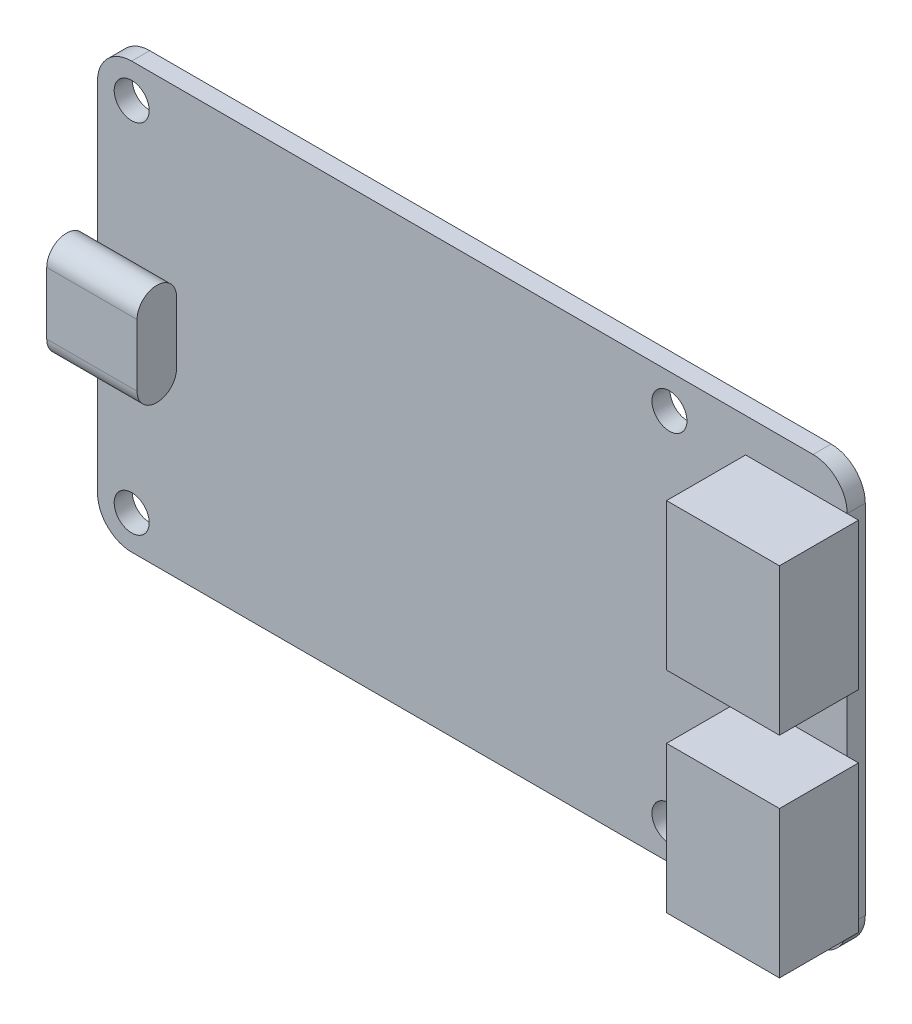
SolidWorks part; units mm, degrees
ref_plane "Plano frontal" through (0, 0, 0) normal (0, 0, 1) x (1, 0, 0)
ref_plane "Plano superior" through (0, 0, 0) normal (0, 1, 0) x (1, 0, 0)
ref_plane "Plano direito" through (0, 0, 0) normal (1, 0, 0) x (0, 0, -1)
sketch "Esboço1" plane through (0, 0, 0) normal (0, 0, 1) x (1, 0, 0)
  line L1 (-30.175, 18.835) -> (30.175, 18.835)
  line L2 (-33.2, 15.81) -> (-33.2, -15.81)
  line L3 (-30.175, -18.835) -> (30.175, -18.835)
  line L4 (33.2, 15.81) -> (33.2, -15.81)
  line L5 (-33.2, 18.835) -> (33.2, -18.835) construction
  line L6 (-33.2, -18.835) -> (33.2, 18.835) construction
  arc A0 (-33.2, -15.81) -> (-30.175, -18.835) centre (-30.175, -15.81) ccw
  arc A1 (30.175, -18.835) -> (33.2, -15.81) centre (30.175, -15.81) ccw
  arc A2 (30.175, 18.835) -> (33.2, 15.81) centre (30.175, 15.81) cw
  arc A3 (-30.175, 18.835) -> (-33.2, 15.81) centre (-30.175, 15.81) ccw
  circle A4 centre (-30.175, 15.81) radius 1.55
  circle A5 centre (-30.175, -15.81) radius 1.55
  circle A6 centre (17.455, 15.81) radius 1.55
  circle A7 centre (17.455, -15.81) radius 1.55
  point P0 (0, 0)
  dimension "D1" = 31.62
  dimension "D5" = 3.1
  dimension "D2" = 37.67
  dimension "D3" = 66.4
  dimension "D4" = 47.63
extrude "Ressalto-extrusão1" add sketch "Esboço1" along normal blind 1.6
sketch "Esboço2" plane through (0, 0, 1.6) normal (0, 0, 1) x (1, 0, 0)
  line L0 (0, 0) -> (18.5434, 0) construction
  line L1 (24.2, 15.81) -> (34.2, 15.81)
  line L2 (24.2, 15.81) -> (24.2, 2.81)
  line L3 (24.2, 2.81) -> (34.2, 2.81)
  line L4 (34.2, 15.81) -> (34.2, 2.81)
  line L5 (24.2, 15.81) -> (34.2, 2.81) construction
  line L6 (24.2, 2.81) -> (34.2, 15.81) construction
  line L7 (24.2, -2.81) -> (34.2, -15.81) construction
  line L8 (24.2, -15.81) -> (34.2, -2.81) construction
  line L9 (34.2, -15.81) -> (34.2, -2.81)
  line L10 (24.2, -2.81) -> (34.2, -2.81)
  line L11 (24.2, -15.81) -> (24.2, -2.81)
  line L12 (24.2, -15.81) -> (34.2, -15.81)
  line L13 (33.2, -15.81) -> (33.2, 15.81) construction
  point P0 (29.2, 9.31)
  point P12 (29.2, -9.31)
  dimension "D1" = 31.62
  dimension "D2" = 13
  dimension "D3" = 10
  dimension "D4" = 1
extrude "Ressalto-extrusão2" add sketch "Esboço2" along normal blind 7
sketch "Esboço3" plane through (-33.2, 0, 0) normal (-1, 0, 0) x (0, 0, 1)
  line L0 (3.35, 2.75) -> (3.35, -2.75) construction
  line L1 (5.1, 2.75) -> (5.1, -2.75)
  line L2 (1.6, 2.75) -> (1.6, -2.75)
  line L3 (0, 15.81) -> (0, -15.81) construction
  line L4 (1.6, 15.81) -> (1.6, -15.81) construction
  arc A0 (5.1, 2.75) -> (1.6, 2.75) centre (3.35, 2.75) ccw
  arc A1 (1.6, -2.75) -> (5.1, -2.75) centre (3.35, -2.75) ccw
  point P2 (3.35, 0)
  point P10 (0, 0)
  dimension "D1" = 1.75
  dimension "D2" = 9
extrude "Ressalto-extrusão3" add sketch "Esboço3" along normal blind 1 and the other way blind 7
